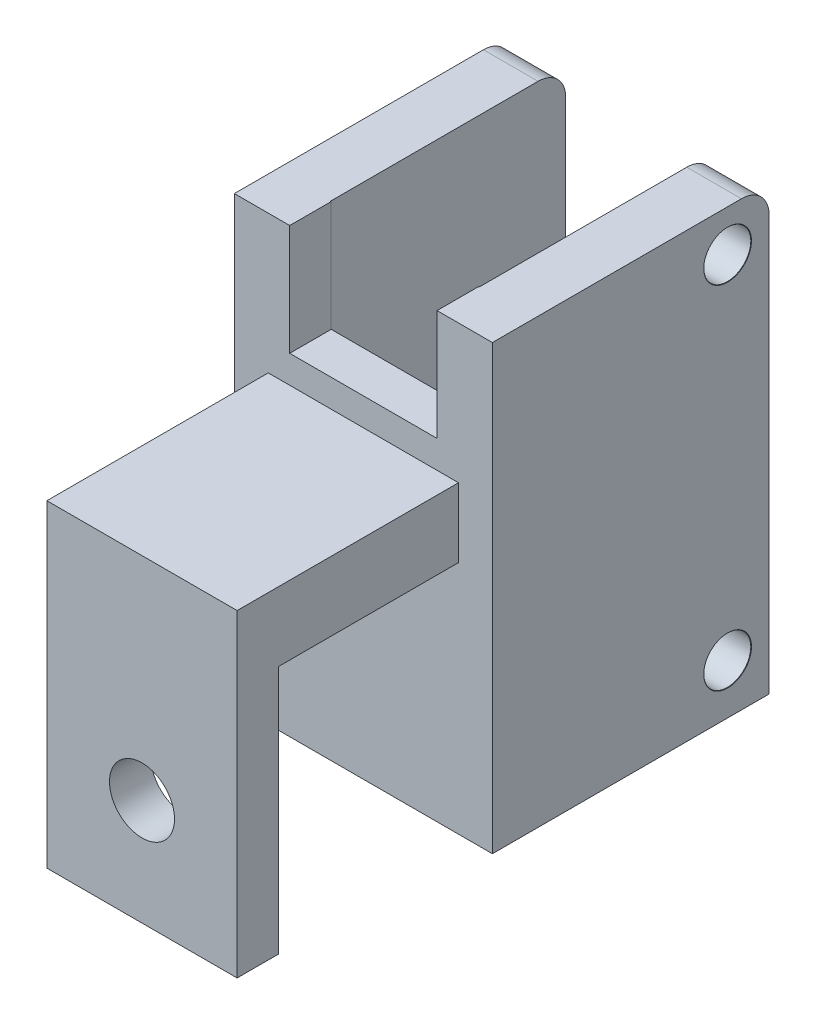
SolidWorks part; units mm, degrees
ref_plane "정면" through (0, 0, 0) normal (0, 0, 1) x (1, 0, 0)
ref_plane "윗면" through (0, 0, 0) normal (0, 1, 0) x (1, 0, 0)
ref_plane "우측면" through (0, 0, 0) normal (1, 0, 0) x (0, 0, -1)
sketch "스케치1" plane through (0, 0, 0) normal (0, 0, 1) x (1, 0, 0)
  line L0 (-77.891, 0) -> (62.6204, 0) construction
  line L1 (0, 64.3726) -> (0, -56.4133) construction
  line L3 (9.325, -16) -> (-9.325, -16)
  line L4 (9.325, -16) -> (9.325, 16)
  line L5 (9.325, 16) -> (-9.325, 16)
  line L6 (-9.325, -16) -> (-9.325, 16)
  line L7 (9.325, -16) -> (-9.325, 16) construction
  line L8 (9.325, 16) -> (-9.325, -16) construction
  point P6 (0, 0)
  dimension "D1" = 18.65
  dimension "D2" = 32
extrude "보스-돌출1" add sketch "스케치1" against normal blind 20
sketch "스케치2" plane through (0, 0, -20) normal (0, 0, -1) x (-1, 0, 0)
  line L0 (9.325, -16) -> (-9.325, -16) construction
  line L4 (-5.375, 16) -> (-5.375, -16)
  line L9 (5.375, 16) -> (5.375, -16)
  line L10 (-5.375, 16) -> (5.375, 16)
  line L12 (-5.375, -16) -> (5.375, -16)
  dimension "D1" = 10.75
  dimension "D2" = 5.375
extrude "컷-돌출2" cut sketch "스케치2" against normal blind 17
sketch "스케치4" plane through (0, 0, 0) normal (0, 0, 1) x (1, 0, 0)
  line L0 (-9.325, 16) -> (-9.325, -16) construction
  line L1 (-5.325, 16) -> (5.325, 16)
  line L2 (-5.325, 16) -> (-5.325, 8)
  line L3 (-5.325, 8) -> (5.325, 8)
  line L4 (5.325, 16) -> (5.325, 8)
  line L5 (9.325, -16) -> (9.325, 16) construction
  line L7 (9.325, 16) -> (-9.325, 16) construction
  dimension "D1" = 4
  dimension "D2" = 4
  dimension "D3" = 8
extrude "컷-돌출3" cut sketch "스케치4" against normal up to next
sketch "스케치7" plane through (9.325, 0, 0) normal (1, 0, 0) x (0, 0, -1)
  point P0 (16.5839, 12.2334)
fillet "필렛1" radius 2 2 edges at (-7.35, 16, -20) (7.35, 16, -20)
sketch "스케치14" plane through (9.325, 0, 0) normal (1, 0, 0) x (0, 0, -1)
  line L0 (20, -16) -> (20, 14) construction
  line L1 (18, 16) -> (0, 16) construction
  circle A0 centre (17, 13) radius 1.7
  circle A1 centre (17, -12.4) radius 1.7
  point P0 (17, 13)
  point P8 (17, -12.4)
  point P17 (38.233, 15.7122)
  dimension "D1" = 3.4
  dimension "D2" = 3
  dimension "D3" = 3
  dimension "D4" = 25.4
hole_wizard "M3 여유 구멍4" positions "스케치14" profile "스케치15" hole size "M3" standard "KS" end condition up to next
sketch "스케치15" plane through (9.325, 13, -17) normal (0, 1, 0) x (0, 0, -1)
  line L0 (0, 0) -> (0, 3.95)
  line L1 (0, 3.95) -> (1.7, 3.95)
  line L2 (1.7, 3.95) -> (1.7, 0.0241)
  line L3 (1.7, 0.0241) -> (1.725, 0)
  line L5 (1.725, 0) -> (0, 0)
  line L6 (-1.7, 0.0241) -> (-1.725, 0) construction
  line L11 (0, -6.35) -> (0, 107.95) construction
  dimension "관통 구멍 지름" = 3.4
  dimension "관통 구멍 깊이" = 3.95
  dimension "표면 카운터싱크 지름" = 3.45
  dimension "표면 카운터싱크 각도" = 92
sketch "스케치18" plane through (0, 0, 0) normal (0, 0, 1) x (1, 0, 0)
  line L0 (5.375, 8) -> (5.375, 16) construction
  line L1 (-6.875, 6) -> (6.875, 6)
  line L2 (-6.875, 6) -> (-6.875, 1)
  line L3 (-6.875, 1) -> (6.875, 1)
  line L4 (6.875, 6) -> (6.875, 1)
  line L5 (-12.1802, 0) -> (13.4887, 0) construction
  line L6 (0, 9.7392) -> (0, -7.5516) construction
  line L8 (-5.375, 16) -> (-5.375, 8) construction
  line L9 (-5.325, 8) -> (5.325, 8) construction
  dimension "D1" = 1.5
  dimension "D2" = 1.5
  dimension "D3" = 5
  dimension "D4" = 2
extrude "보스-돌출2" add sketch "스케치18" along normal blind 16
sketch "스케치19" plane through (0, 1, 0) normal (0, -1, 0) x (1, 0, 0)
  line L0 (6.875, 16) -> (6.875, 0) construction
  line L1 (-6.875, 16) -> (6.875, 16)
  line L2 (-6.875, 16) -> (-6.875, 13)
  line L3 (-6.875, 13) -> (6.875, 13)
  line L4 (6.875, 16) -> (6.875, 13)
  line L5 (-9.325, 0) -> (9.325, 0) construction
  dimension "D1" = 13
extrude "보스-돌출3" add sketch "스케치19" along normal blind 18
sketch "스케치20" plane through (0, 0, 16) normal (0, 0, 1) x (1, 0, 0)
  circle A0 centre (0, -9.3206) radius 2.35
  dimension "D1" = 4.7
extrude "컷-돌출4" cut sketch "스케치20" against normal up to next
